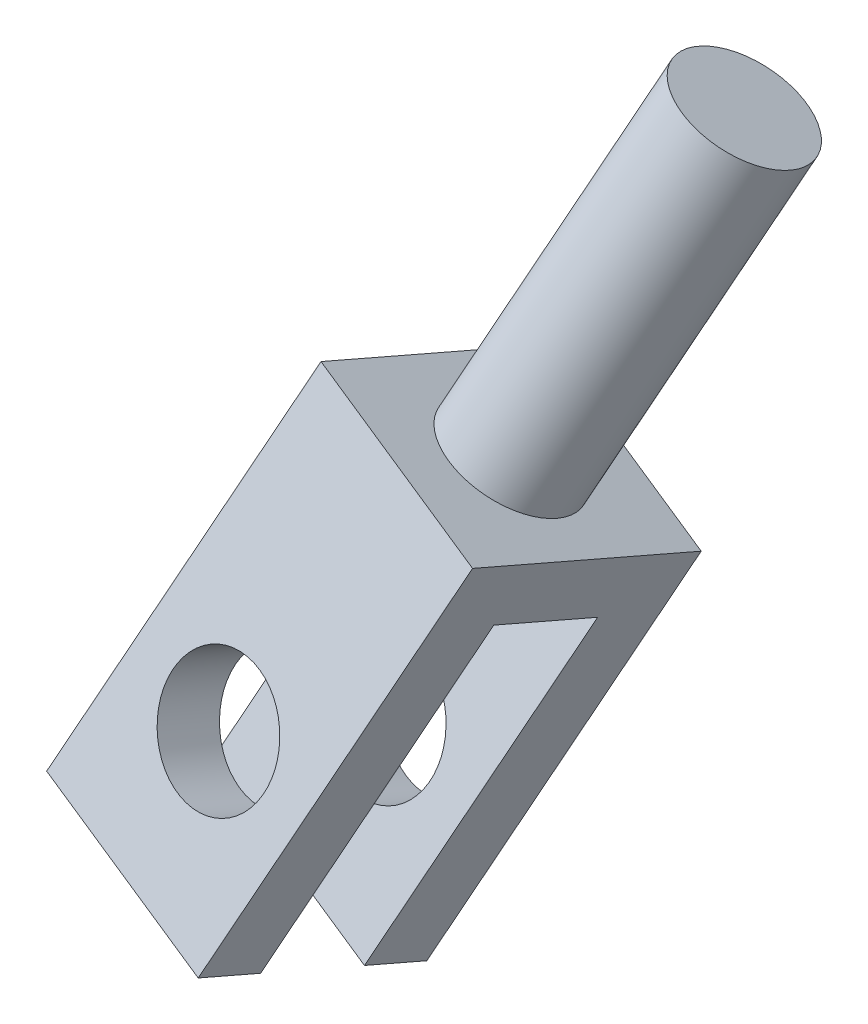
SolidWorks part; units mm, degrees
ref_plane "Front Plane" through (0, 0, 0) normal (0, 0, 1) x (1, 0, 0)
ref_plane "Top Plane" through (0, 0, 0) normal (0, 1, 0) x (1, 0, 0)
ref_plane "Right Plane" through (0, 0, 0) normal (1, 0, 0) x (0, 0, -1)
sketch "Sketch2" plane through (707.5622, 137.847, -295.1758) normal (-0.9319, 0.3048, -0.1966) x (0.3542, 0.8818, -0.3113)
  line L0 (-166.5458, -35.4961) -> (-149.5458, -35.4961)
  line L1 (-149.5458, -35.4961) -> (-149.5458, -40.4961)
  line L2 (-149.5458, -40.4961) -> (-166.5458, -40.4961)
  line L3 (-166.5458, -40.4961) -> (-166.5458, -43.4961)
  line L4 (-166.5458, -43.4961) -> (-146.5458, -43.4961)
  line L5 (-146.5458, -43.4961) -> (-146.5458, -32.4961)
  line L6 (-146.5458, -32.4961) -> (-166.5458, -32.4961)
  line L7 (-166.5458, -32.4961) -> (-166.5458, -35.4961)
  dimension "D1" = 5
  dimension "D2" = 3
  dimension "D3" = 3
  dimension "D4" = 20
  dimension "D5" = 3
  dimension "D6" = 20
extrude "Boss-Extrude1" add sketch "Sketch2" along normal blind 10 contours L4 L5 L6 L7 L0 L1 L2 L3
sketch "Sketch3" plane through (18.8265, -86.3012, -223.022) normal (0.0785, -0.3598, -0.9297) x (-0.9969, -0.0283, -0.0732)
  line L0 (-625.2036, 98.844) -> (-619.1642, 82.9529) construction
  line L2 (-619.1642, 82.9529) -> (-628.5119, 79.4003) construction
  circle A0 centre (-626.3249, 87.72) radius 3
  dimension "D1" = 6
  dimension "D2" = 5
  dimension "D3" = 7
extrude "Cut-Extrude1" cut sketch "Sketch3" against normal through all both and the other way through all contours A0
sketch "Sketch4" plane through (112.4483, 279.9875, -98.8523) normal (0.3542, 0.8818, -0.3113) x (0.9352, -0.334, 0.1179)
  line L0 (568.1702, 200.9033) -> (578.1349, 200.0641) construction
  line L4 (567.247, 189.9421) -> (568.1702, 200.9033) construction
  circle A0 centre (572.6909, 195.0031) radius 3
  dimension "D1" = 6
  dimension "D2" = 5.5
  dimension "D3" = 5
extrude "Boss-Extrude2" add sketch "Sketch4" along normal blind 17
